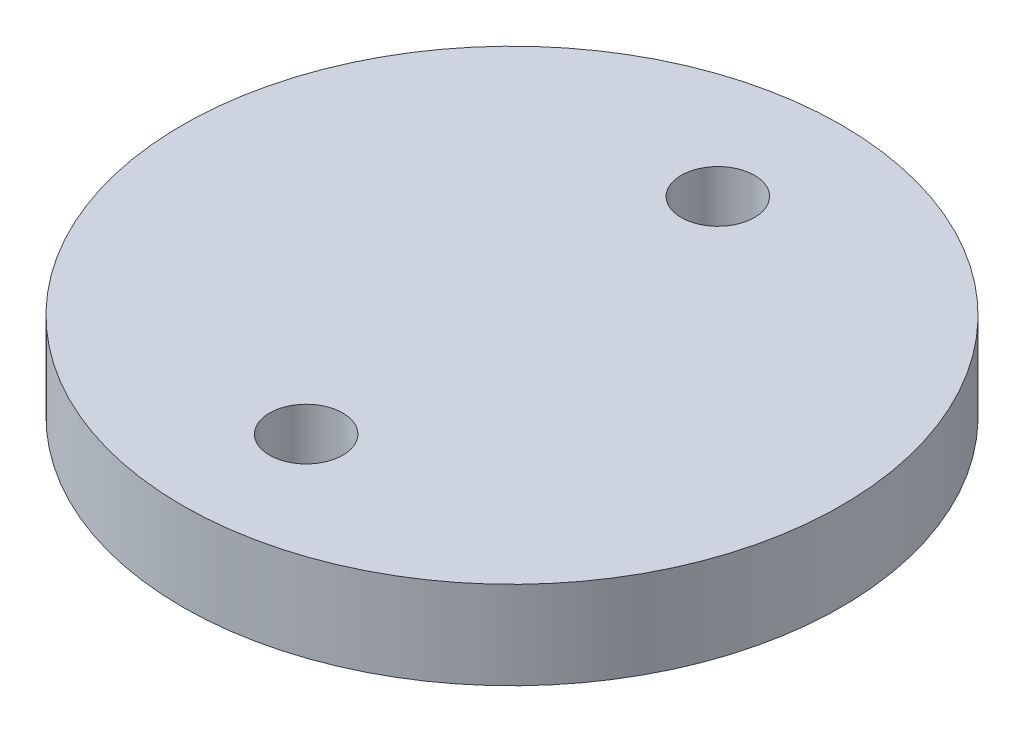
SolidWorks part; units mm, degrees
ref_plane "Front Plane" through (0, 0, 0) normal (0, 0, 1) x (1, 0, 0)
ref_plane "Top Plane" through (0, 0, 0) normal (0, 1, 0) x (1, 0, 0)
ref_plane "Right Plane" through (0, 0, 0) normal (1, 0, 0) x (0, 0, -1)
sketch "Sketch1" plane through (0, 0, 0) normal (0, 1, 0) x (1, 0, 0)
  line L0 (0, 0) -> (0, 7.1393) construction
  line L1 (0, 0) -> (0, -7.1393) construction
  circle A0 centre (0, 0) radius 11.43
  circle A1 centre (0, 7.1393) radius 1.27
  circle A2 centre (0, -7.1393) radius 1.27
  dimension "D2" = 2.54
  dimension "D3" = 22.86
  dimension "D1" = 14.2786
extrude "Boss-Extrude1" add sketch "Sketch1" along normal blind 3.048
